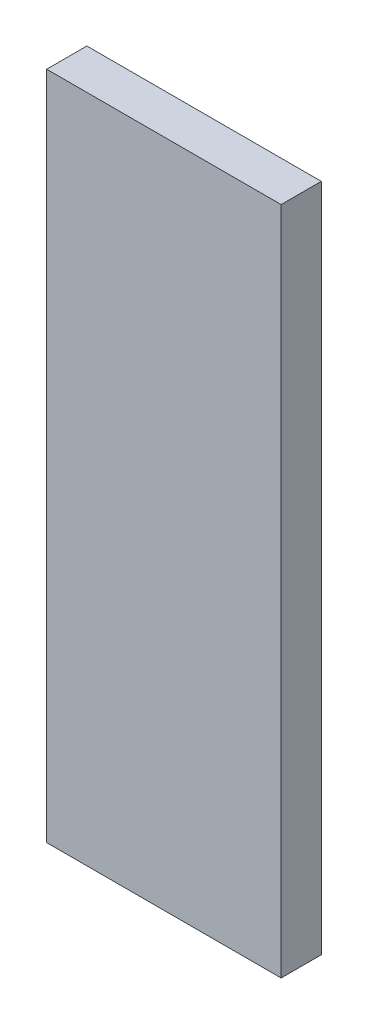
SolidWorks part; units mm, degrees
ref_plane "Front Plane" through (0, 0, 0) normal (0, 0, 1) x (1, 0, 0)
ref_plane "Top Plane" through (0, 0, 0) normal (0, 1, 0) x (1, 0, 0)
ref_plane "Right Plane" through (0, 0, 0) normal (1, 0, 0) x (0, 0, -1)
sketch "Sketch1" plane through (0, 0, 0) normal (0, 0, 1) x (1, 0, 0)
  line L1 (8.75, 25) -> (-8.75, 25)
  line L2 (8.75, 25) -> (8.75, -25)
  line L3 (8.75, -25) -> (-8.75, -25)
  line L4 (-8.75, 25) -> (-8.75, -25)
  line L5 (8.75, 25) -> (-8.75, -25) construction
  line L6 (8.75, -25) -> (-8.75, 25) construction
  point P0 (0, 0)
  dimension "D1" = 50
  dimension "D2" = 17.5
extrude "Boss-Extrude1" add sketch "Sketch1" along normal blind 3
